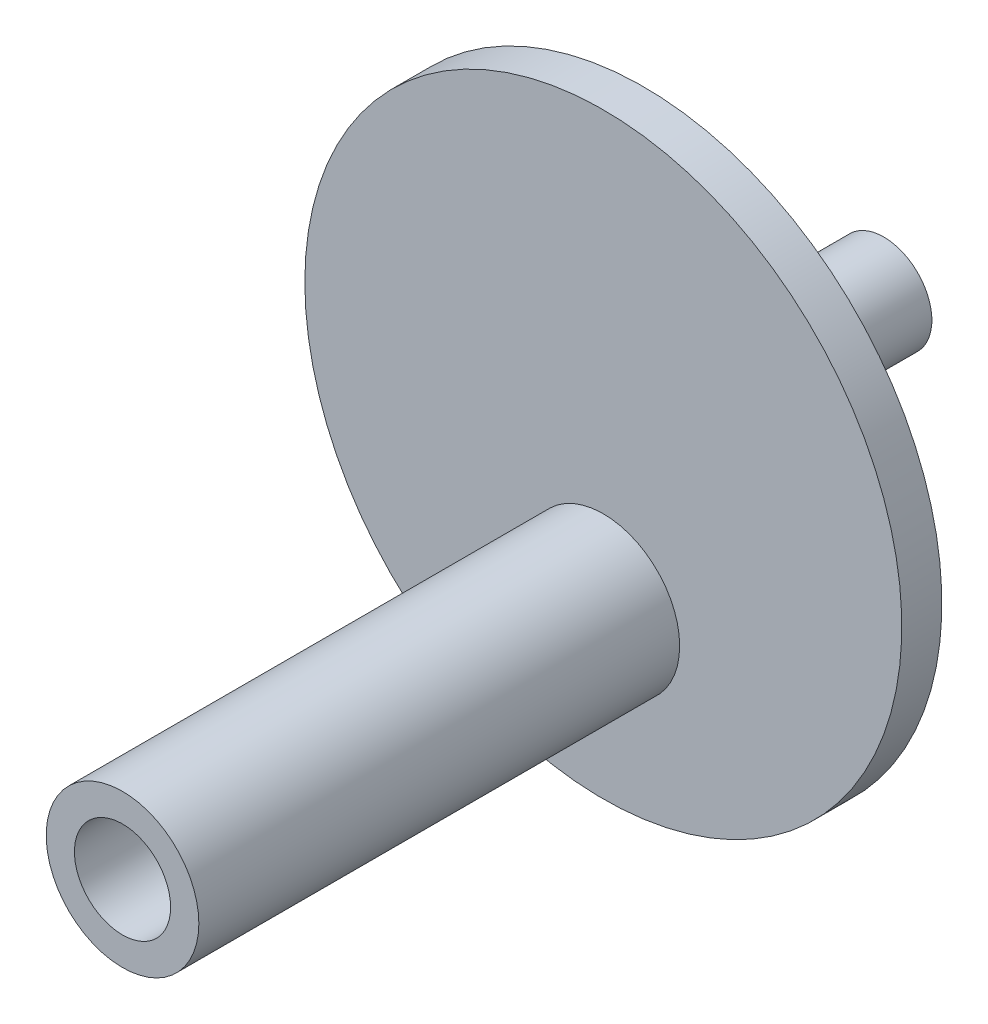
SolidWorks part; units mm, degrees
ref_plane "Front Plane" through (0, 0, 0) normal (0, 0, 1) x (1, 0, 0)
ref_plane "Top Plane" through (0, 0, 0) normal (0, 1, 0) x (1, 0, 0)
ref_plane "Right Plane" through (0, 0, 0) normal (1, 0, 0) x (0, 0, -1)
sketch "Sketch1" plane through (0, 0, 0) normal (1, 0, 0) x (0, 0, -1)
  line L0 (0, 0) -> (35.7946, 0) construction
  line L1 (0, 8) -> (0, 37.25)
  line L2 (0, 37.25) -> (-5, 37.25)
  line L3 (-5, 37.25) -> (-5, 0)
  line L4 (30, 0) -> (-5, 0)
  line L5 (0, 8) -> (15.1, 8)
  line L6 (15.1, 8) -> (15.1, 6)
  line L7 (15.1, 6) -> (30, 6)
  line L8 (30, 6) -> (30, 0)
  line L9 (0, 8) -> (0, -0.3127) construction
  dimension "D1" = 5
  dimension "D2" = 15.1
  dimension "D3" = 37.25
  dimension "D4" = 6
  dimension "30" = 30
  dimension "D5" = 8
revolve "Revolve1" add sketch "Sketch1" angle 360 about L4
sketch "Sketch2" plane through (0, 0, 5) normal (0, 0, 1) x (1, 0, 0)
  line L0 (0, 0) -> (0, -15.9375) construction
  circle A0 centre (0, -15.9375) radius 9.525
  circle A1 centre (0, -15.9375) radius 6
  dimension "D1" = 19.05
  dimension "D2" = 12
  dimension "D3" = 15.9375
extrude "Boss-Extrude1" add sketch "Sketch2" along normal blind 60
sketch "Sketch3" plane through (0, 0, 0) normal (0, 0, -1) x (-1, 0, 0)
  line L0 (0, 0) -> (0, 25.9724) construction
sketch "Sketch4" plane through (0, 0, 5) normal (0, 0, 1) x (1, 0, 0)
  line L0 (0, 0) -> (0, 37.25) construction
  line L1 (0, 0) -> (0, -106.648) construction
  circle A0 centre (0, 0) radius 37.25 construction
